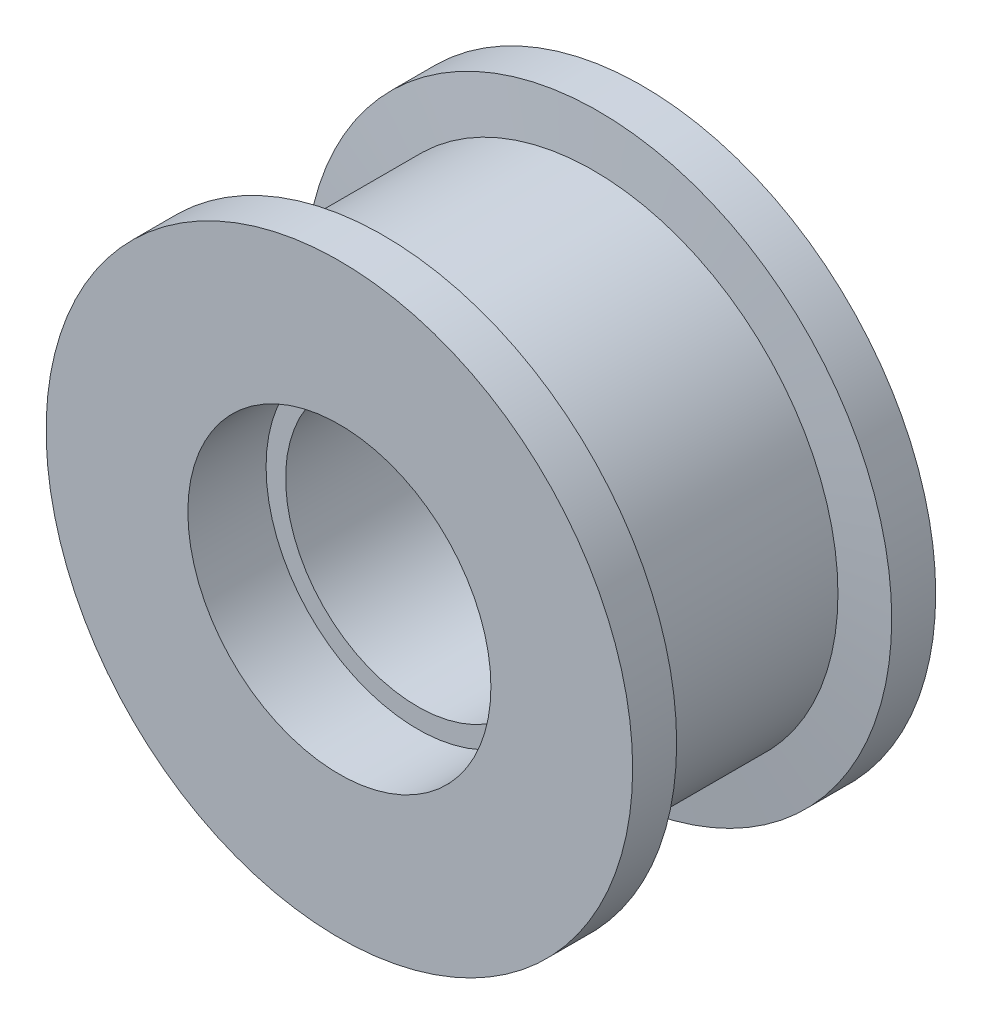
SolidWorks part; units mm, degrees
material "AISI 1045 钢，冷拔"
ref_plane "前视基准面" through (0, 0, 0) normal (0, 0, 1) x (1, 0, 0)
ref_plane "上视基准面" through (0, 0, 0) normal (0, 1, 0) x (1, 0, 0)
ref_plane "右视基准面" through (0, 0, 0) normal (1, 0, 0) x (0, 0, -1)
ref_plane "基准面4" through (0, 0, 0) normal (1, 0, 0) x (0, 0, -1)
sketch "草图2" plane through (0, 0, 0) normal (1, 0, 0) x (0, 0, -1)
  line L0 (-4235.1784, -7413.9832) -> (-4120.1784, -7413.9832) construction
  line L3 (-4202.9152, -7473.9832) -> (-4193.9152, -7473.9832)
  line L4 (-4193.9152, -7473.9832) -> (-4192.9152, -7463.9832)
  line L5 (-4192.9152, -7463.9832) -> (-4150.9152, -7463.9832)
  line L6 (-4150.9152, -7463.9832) -> (-4149.9152, -7473.9832)
  line L7 (-4149.9152, -7473.9832) -> (-4140.9152, -7473.9832)
  line L8 (-4140.9152, -7473.9832) -> (-4140.9152, -7444.9832)
  line L9 (-4140.9152, -7444.9832) -> (-4156.9152, -7444.9832)
  line L10 (-4156.9152, -7444.9832) -> (-4156.9152, -7440.9832)
  line L11 (-4156.9152, -7440.9832) -> (-4186.9152, -7440.9832)
  line L12 (-4186.9152, -7440.9832) -> (-4186.9152, -7444.9832)
  line L13 (-4186.9152, -7444.9832) -> (-4202.9152, -7444.9832)
  line L14 (-4202.9152, -7444.9832) -> (-4202.9152, -7473.9832)
  dimension "D1" = 31
  dimension "D2" = 16
  dimension "D3" = 16
  dimension "D4" = 9
  dimension "D5" = 10
  dimension "D6" = 50
  dimension "D7" = 10
  dimension "D8" = 9
  dimension "D9" = 10
  dimension "D10" = 10
  dimension "D11" = 42
  dimension "D12" = 4
  dimension "D13" = 4
revolve "旋转2" add sketch "草图2" angle 360 about L0
